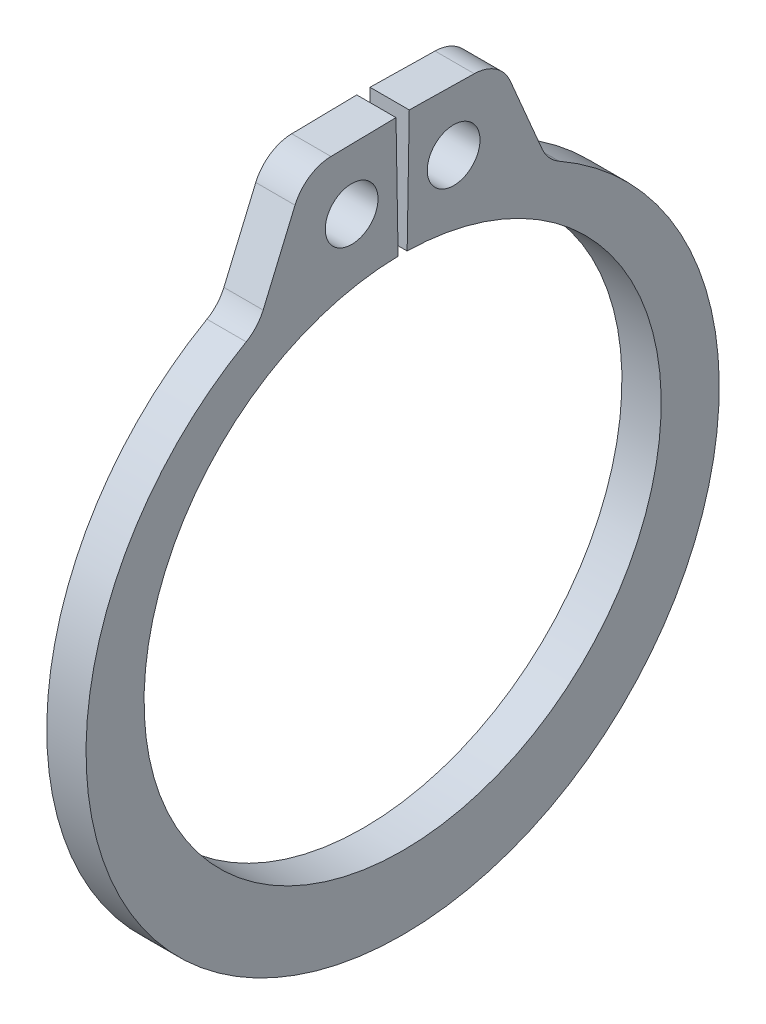
SolidWorks part; units mm, degrees
material "Cast Carbon Steel"
ref_plane "Front" through (0, 0, 0) normal (0, 0, 1) x (1, 0, 0)
ref_plane "Top" through (0, 0, 0) normal (0, 1, 0) x (1, 0, 0)
ref_plane "Right" through (0, 0, 0) normal (1, 0, 0) x (0, 0, -1)
sketch "Sketch1" plane through (0, 0, 0) normal (1, 0, 0) x (0, 0, -1)
  line L0 (0, 0) -> (0, 5.8547) construction
  line L1 (-0.1022, 5.8538) -> (-0.1501, 8.5966)
  line L2 (0.1501, 8.5966) -> (2.2071, 8.5607)
  line L3 (2.2071, 8.5607) -> (3.2813, 6.0365)
  line L4 (0.1022, 5.8538) -> (0.1501, 8.5966)
  line L5 (-0.1501, 8.5966) -> (-2.2071, 8.5607)
  line L6 (-2.2071, 8.5607) -> (-3.2813, 6.0365)
  line L7 (-3.2813, 6.0365) -> (-2.7961, 5.1439) construction
  line L8 (3.2813, 6.0365) -> (2.7961, 5.1439) construction
  line L9 (0, -5.8547) -> (0, -7.5057) construction
  line L10 (-2.2071, 8.5607) -> (-0.1022, 5.8538) construction
  line L11 (0, 5.8547) -> (0, 8.5979) construction
  circle A0 centre (0, 0) radius 5.8547 construction
  arc A1 (-0.1022, 5.8538) -> (0.1022, 5.8538) centre (0, 0) ccw
  circle A3 centre (0, 0) radius 9.5885 construction
  circle A4 centre (-1.1547, 7.2072) radius 0.5969
  circle A5 centre (1.1547, 7.2072) radius 0.5969
  arc A6 (-3.2813, 6.0365) -> (3.2813, 6.0365) centre (0, -0.3371) ccw
  point P0 (0, -7.5057)
  dimension "A" = 11.7094
  dimension "D2" = 2.0574
  dimension "L" = 19.177
  dimension "Hole" = 1.1938
  dimension "Smin" = 1.016
  dimension "Smax" = 1.651
  dimension "H" = 2.7432
  dimension "Angle" = 1
extrude "Extrude1" add sketch "Sketch1" along normal mid plane 0.889
fillet "Fillet1" radius 0.9017 4 edges at (0, 6.0365, 3.2813) (0, 6.0365, -3.2813) (0, 8.5607, 2.2071) (0, 8.5607, -2.2071)
sketch "Sketch2" plane through (0, 0, 0) normal (0, 0, 1) x (1, 0, 0)
  line L0 (-3.829, 0) -> (9.5059, 0)
  line L1 (9.5059, 0) -> (9.506, -6.35)
  line L2 (-0.4953, -6.35) -> (-3.4227, -6.35)
  line L3 (9.506, -6.35) -> (0.4953, -6.35)
  line L4 (0.4953, -6.35) -> (0.4953, -5.9436)
  line L5 (0.4953, -5.9436) -> (-0.4953, -5.9436)
  line L6 (-0.4953, -5.9436) -> (-0.4953, -6.35)
  line L7 (-0.4953, -6.35) -> (-3.829, -6.35) construction
  line L8 (-3.829, -6.35) -> (-3.829, 0) construction
  line L9 (9.5059, 0) -> (76.391, 0) construction
  line L10 (-3.4227, -6.35) -> (-3.829, -5.9436)
  line L11 (-3.829, -5.9436) -> (-3.829, 0)
  point P10 (0, -5.9436)
  dimension "D1" = 45
  dimension "Dg" = 11.8872
  dimension "Ds" = 12.7
  dimension "W" = 0.9906
  dimension "D2" = 13.335
  dimension "D3" = 3.3337
revolve "Revolve1" [suppressed] add sketch "Sketch2" angle 360 about L9
delete or keep bodies "Body-Delete1" [suppressed] type delete bodies bodies 122
equation "\"D2@Sketch2\" = \"D1@Extrude1\"*15"
equation "\"D3@Sketch2\" = \"D2@Sketch2\"/4"
equation "\"D2@Sketch1\" = \"H@Sketch1\"*.75"
